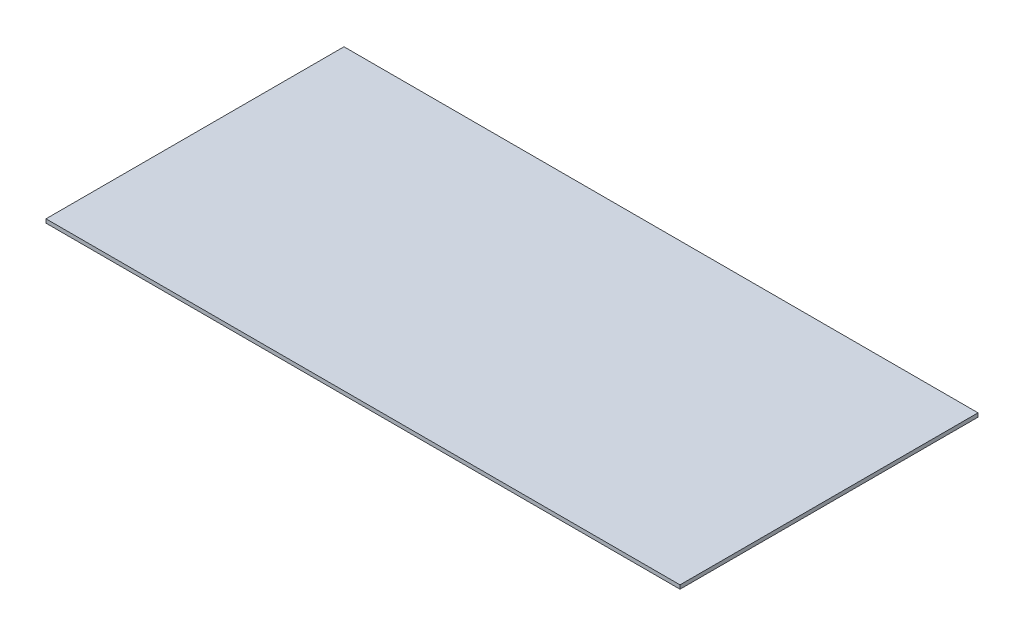
SolidWorks part; units mm, degrees
ref_plane "Front Plane" through (0, 0, 0) normal (0, 0, 1) x (1, 0, 0)
ref_plane "Top Plane" through (0, 0, 0) normal (0, 1, 0) x (1, 0, 0)
ref_plane "Right Plane" through (0, 0, 0) normal (1, 0, 0) x (0, 0, -1)
sketch "Sketch1" plane through (0, 0, 0) normal (0, 1, 0) x (1, 0, 0)
  line L0 (170, 117.5) -> (250, 117.5)
  line L1 (250, 117.5) -> (250, -117.5)
  line L2 (250, -117.5) -> (-250, -117.5)
  line L3 (-250, -117.5) -> (-250, 117.5)
  line L4 (-250, 117.5) -> (170, 117.5)
extrude "Boss-Extrude1" add sketch "Sketch1" along normal blind 3
